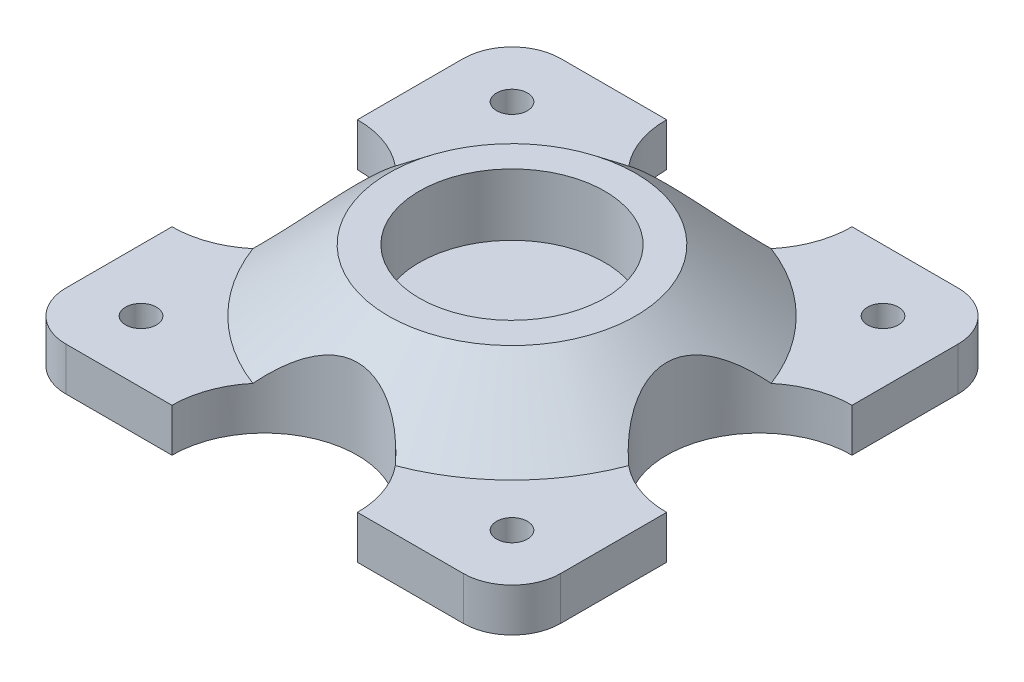
SolidWorks part; units mm, degrees
ref_plane "Front Plane" through (0, 0, 0) normal (0, 0, 1) x (1, 0, 0)
ref_plane "Top Plane" through (0, 0, 0) normal (0, 1, 0) x (1, 0, 0)
ref_plane "Right Plane" through (0, 0, 0) normal (1, 0, 0) x (0, 0, -1)
sketch "Sketch1" plane through (0, 0, 0) normal (0, 1, 0) x (1, 0, 0)
  line L1 (40.8, 50.8) -> (-40.8, 50.8)
  line L2 (50.8, 40.8) -> (50.8, -40.8)
  line L3 (40.8, -50.8) -> (-40.8, -50.8)
  line L4 (-50.8, 40.8) -> (-50.8, -40.8)
  line L5 (50.8, 50.8) -> (-50.8, -50.8) construction
  line L6 (50.8, -50.8) -> (-50.8, 50.8) construction
  arc A0 (-40.8, 50.8) -> (-50.8, 40.8) centre (-40.8, 40.8) ccw
  arc A1 (50.8, -40.8) -> (40.8, -50.8) centre (40.8, -40.8) cw
  arc A2 (40.8, 50.8) -> (50.8, 40.8) centre (40.8, 40.8) cw
  arc A3 (-40.8, -50.8) -> (-50.8, -40.8) centre (-40.8, -40.8) cw
  point P0 (0, 0)
  dimension "D3" = 10
  dimension "D1" = 101.6
  dimension "D2" = 101.6
extrude "Boss-Extrude1" add sketch "Sketch1" along normal blind 8.89
sketch "Sketch2" plane through (0, 0, 0) normal (0, 0, 1) x (1, 0, 0)
  line L0 (0, 8.89) -> (0, 21.59)
  line L1 (40.8, 8.89) -> (-40.8, 8.89) construction
  line L2 (0, 21.59) -> (-25.4, 21.59)
  line L3 (-25.4, 21.59) -> (-41.28, 8.89)
  line L4 (-41.28, 8.89) -> (0, 8.89)
  line L5 (40.8, 0) -> (-40.8, 0) construction
  dimension "D1" = 21.59
  dimension "D2" = 25.4
  dimension "D3" = 41.28
revolve "Revolve1" add sketch "Sketch2" angle 360 about L0
sketch "Sketch3" plane through (0, 21.59, 0) normal (0, 1, 0) x (1, 0, 0)
  line L0 (40.8, 50.8) -> (-40.8, 50.8) construction
  line L1 (50.8, -40.8) -> (50.8, 40.8) construction
  line L2 (-50.8, 40.8) -> (-50.8, -40.8) construction
  line L3 (-40.8, -50.8) -> (40.8, -50.8) construction
  line L4 (-50.8, 19.05) -> (-50.8, -19.05)
  line L5 (-38.1, -38.1) -> (38.1, -38.1) construction
  line L6 (-38.1, -38.1) -> (-38.1, 38.1) construction
  line L7 (-38.1, 38.1) -> (38.1, 38.1) construction
  line L8 (38.1, -38.1) -> (38.1, 38.1) construction
  line L9 (-38.1, -38.1) -> (38.1, 38.1) construction
  line L10 (-38.1, 38.1) -> (38.1, -38.1) construction
  line L11 (-19.05, 50.8) -> (19.05, 50.8)
  line L12 (50.8, 19.05) -> (50.8, -19.05)
  line L13 (-19.05, -50.8) -> (19.05, -50.8)
  circle A0 centre (0, 0) radius 19.05
  arc A1 (-19.05, 50.8) -> (19.05, 50.8) centre (0, 50.8) ccw
  arc A2 (50.8, 19.05) -> (50.8, -19.05) centre (50.8, 0) ccw
  arc A3 (-50.8, -19.05) -> (-50.8, 19.05) centre (-50.8, 0) ccw
  arc A4 (19.05, -50.8) -> (-19.05, -50.8) centre (0, -50.8) ccw
  circle A5 centre (-38.1, 38.1) radius 3.175
  circle A6 centre (38.1, 38.1) radius 3.175
  circle A7 centre (38.1, -38.1) radius 3.175
  circle A8 centre (-38.1, -38.1) radius 3.175
  dimension "D1" = 38.1
  dimension "D5" = 6.35
  dimension "D2" = 76.2
  dimension "D3" = 12.7
  dimension "D4" = 12.7
extrude "Cut-Extrude1" cut sketch "Sketch3" against normal through all
sketch "Sketch4" plane through (0, 0, 0) normal (0, -1, 0) x (1, 0, 0)
  circle A0 centre (0, 0) radius 19.05 construction
  circle A1 centre (0, 0) radius 19.05
extrude "Boss-Extrude3" add sketch "Sketch4" against normal up to surface (8.89 mm away) up to face at (38.1, 8.89, 41.275)
